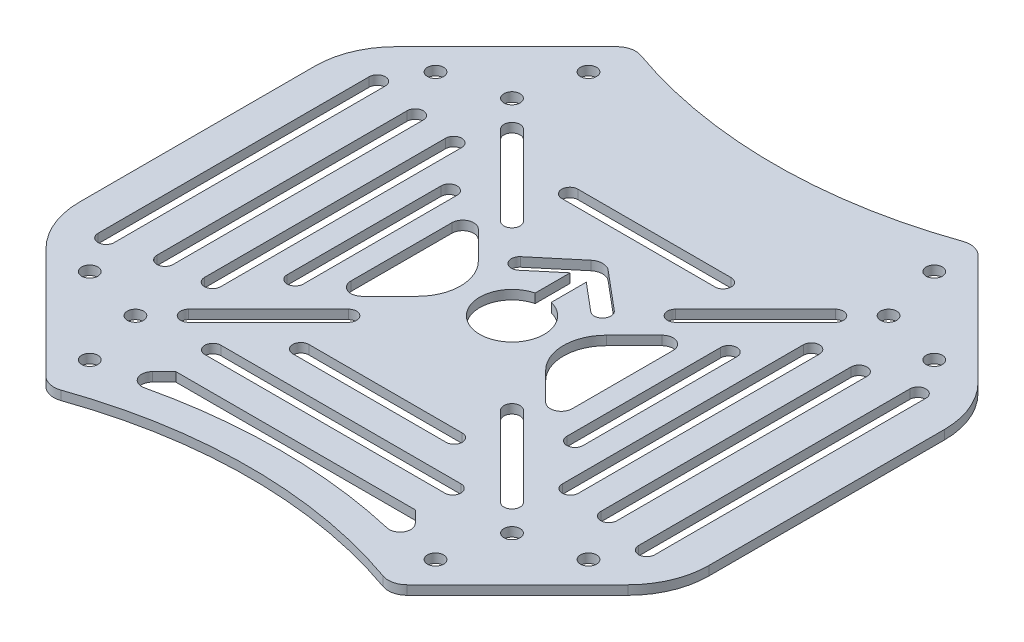
SolidWorks part; units mm, degrees
ref_plane "前基準面" through (0, 0, 0) normal (0, 0, 1) x (1, 0, 0)
ref_plane "上基準面" through (0, 0, 0) normal (0, 1, 0) x (1, 0, 0)
ref_plane "右基準面" through (0, 0, 0) normal (1, 0, 0) x (0, 0, -1)
sketch "草圖1" plane through (0, 0, 0) normal (0, 1, 0) x (1, 0, 0)
  line L0 (-88.3224, -92.0235) -> (-10.6127, -92.0235) construction
  line L1 (-96.5414, 45.9038) -> (-96.5414, -104.0962) construction
  line L2 (0, 5.7817) -> (0, -5.7817) construction
  line L3 (-13.0005, 0) -> (13.0005, 0) construction
  line L4 (-14.25, 25) -> (14.25, 25) construction
  line L5 (-14.25, 26.5) -> (14.25, 26.5)
  line L6 (-14.25, 23.5) -> (14.25, 23.5)
  line L7 (-14.25, -25) -> (14.25, -25) construction
  line L8 (-14.25, -26.5) -> (14.25, -26.5)
  line L9 (-14.25, -23.5) -> (14.25, -23.5)
  line L10 (-47.2341, 47.2341) -> (47.2341, -47.2341) construction
  line L11 (47.2341, 47.2341) -> (-47.2341, -47.2341) construction
  line L12 (-30.052, 30.052) -> (-15.2028, 15.2028) construction
  line L13 (-28.9914, 31.1127) -> (-14.1421, 16.2635)
  line L14 (-31.1127, 28.9914) -> (-16.2635, 14.1421)
  line L15 (30.052, 30.052) -> (15.2028, 15.2028) construction
  line L16 (28.9914, 31.1127) -> (14.1421, 16.2635)
  line L17 (31.1127, 28.9914) -> (16.2635, 14.1421)
  line L18 (30.052, -30.052) -> (15.2028, -15.2028) construction
  line L19 (28.9914, -31.1127) -> (14.1421, -16.2635)
  line L20 (31.1127, -28.9914) -> (16.2635, -14.1421)
  line L21 (-30.052, -30.052) -> (-15.2028, -15.2028) construction
  line L22 (-28.9914, -31.1127) -> (-14.1421, -16.2635)
  line L23 (-31.1127, -28.9914) -> (-16.2635, -14.1421)
  line L24 (-33.25, 22.4) -> (-33.25, -22.4) construction
  line L25 (-31.75, 22.4) -> (-31.75, -22.4)
  line L26 (-34.75, 22.4) -> (-34.75, -22.4)
  line L27 (-41.25, 23.25) -> (-41.25, -23.25) construction
  line L28 (-39.75, 23.25) -> (-39.75, -23.25)
  line L29 (-42.75, 23.25) -> (-42.75, -23.25)
  line L30 (-50.25, 25.2) -> (-50.25, -25.2) construction
  line L31 (-48.75, 25.2) -> (-48.75, -25.2)
  line L32 (-51.75, 25.2) -> (-51.75, -25.2)
  line L33 (50.25, 25.2) -> (50.25, -25.2) construction
  line L34 (48.75, 25.2) -> (48.75, -25.2)
  line L35 (51.75, 25.2) -> (51.75, -25.2)
  line L36 (41.25, 23.25) -> (41.25, -23.25) construction
  line L37 (39.75, 23.25) -> (39.75, -23.25)
  line L38 (42.75, 23.25) -> (42.75, -23.25)
  line L39 (33.25, 22.4) -> (33.25, -22.4) construction
  line L40 (31.75, 22.4) -> (31.75, -22.4)
  line L41 (34.75, 22.4) -> (34.75, -22.4)
  line L42 (-26, 14.3) -> (-26, -14.3) construction
  line L43 (-24.5, 14.3) -> (-24.5, -14.3)
  line L44 (-27.5, 14.3) -> (-27.5, -14.3)
  line L45 (-1.5, 5.8095) -> (-1.5, 12.3095)
  line L46 (-1.5, 12.3095) -> (-6.7013, 7.9451)
  line L47 (-8.6939, 10.3198) -> (-1.607, 16.2665)
  line L48 (8.6939, 10.3198) -> (1.607, 16.2665)
  line L49 (1.5, 5.8095) -> (1.5, 12.3095)
  line L50 (1.5, 12.3095) -> (6.7013, 7.9451)
  line L51 (26, 14.3) -> (26, -14.3) construction
  line L52 (24.5, 14.3) -> (24.5, -14.3)
  line L53 (27.5, 14.3) -> (27.5, -14.3)
  line L54 (-22.3, -33.3) -> (22.3, -33.3) construction
  line L55 (-22.3, -31.8) -> (22.3, -31.8)
  line L56 (-22.3, -34.8) -> (22.3, -34.8)
  line L57 (-31.9883, -54.6323) -> (-58.5, -28.1206)
  line L58 (-58.5, -28.1206) -> (-58.5, 28.1206)
  line L59 (31.9883, -54.6323) -> (58.5, -28.1206)
  line L60 (58.5, -28.1206) -> (58.5, 28.1206)
  line L61 (-31.9883, 54.6323) -> (-58.5, 28.1206)
  line L62 (31.9883, 54.6323) -> (58.5, 28.1206)
  line L63 (20.5663, -9.3678) -> (20.5663, 9.3678)
  line L64 (17.0742, 10.8143) -> (11.9044, 5.6446)
  line L65 (17.0742, -10.8143) -> (11.9044, -5.6446)
  line L66 (-17.0742, -10.8143) -> (-11.9044, -5.6446)
  line L67 (-17.0742, 10.8143) -> (-11.9044, 5.6446)
  line L68 (-20.5663, -9.3678) -> (-20.5663, 9.3678)
  line L69 (-22.2619, -40.2376) -> (22.2619, -40.2376)
  line L70 (22.2619, -40.2376) -> (24.4317, -42.4074)
  line L71 (-22.2619, -40.2376) -> (-24.4317, -42.4074)
  line L72 (32.138, 46.3508) -> (46.3508, 32.138) construction
  line L73 (3.7413, -66.2623) -> (66.2623, -3.7413) construction
  arc A0 (-14.25, 26.5) -> (-14.25, 23.5) centre (-14.25, 25) ccw
  arc A1 (14.25, 23.5) -> (14.25, 26.5) centre (14.25, 25) ccw
  arc A2 (-14.25, -26.5) -> (-14.25, -23.5) centre (-14.25, -25) cw
  arc A3 (14.25, -23.5) -> (14.25, -26.5) centre (14.25, -25) cw
  circle A4 centre (-35.0018, 35.0018) radius 1.5
  circle A5 centre (35.0018, -35.0018) radius 1.5
  circle A6 centre (-35.0018, -35.0018) radius 1.5
  circle A7 centre (35.0018, 35.0018) radius 1.5
  arc A8 (-28.9914, 31.1127) -> (-31.1127, 28.9914) centre (-30.052, 30.052) ccw
  arc A9 (-16.2635, 14.1421) -> (-14.1421, 16.2635) centre (-15.2028, 15.2028) ccw
  arc A10 (28.9914, 31.1127) -> (31.1127, 28.9914) centre (30.052, 30.052) cw
  arc A11 (16.2635, 14.1421) -> (14.1421, 16.2635) centre (15.2028, 15.2028) cw
  arc A12 (28.9914, -31.1127) -> (31.1127, -28.9914) centre (30.052, -30.052) ccw
  arc A13 (16.2635, -14.1421) -> (14.1421, -16.2635) centre (15.2028, -15.2028) ccw
  arc A14 (-28.9914, -31.1127) -> (-31.1127, -28.9914) centre (-30.052, -30.052) cw
  arc A15 (-16.2635, -14.1421) -> (-14.1421, -16.2635) centre (-15.2028, -15.2028) cw
  arc A16 (-31.75, 22.4) -> (-34.75, 22.4) centre (-33.25, 22.4) ccw
  arc A17 (-34.75, -22.4) -> (-31.75, -22.4) centre (-33.25, -22.4) ccw
  arc A18 (-39.75, 23.25) -> (-42.75, 23.25) centre (-41.25, 23.25) ccw
  arc A19 (-42.75, -23.25) -> (-39.75, -23.25) centre (-41.25, -23.25) ccw
  arc A20 (-48.75, 25.2) -> (-51.75, 25.2) centre (-50.25, 25.2) ccw
  arc A21 (-51.75, -25.2) -> (-48.75, -25.2) centre (-50.25, -25.2) ccw
  arc A22 (48.75, 25.2) -> (51.75, 25.2) centre (50.25, 25.2) cw
  arc A23 (51.75, -25.2) -> (48.75, -25.2) centre (50.25, -25.2) cw
  arc A24 (39.75, 23.25) -> (42.75, 23.25) centre (41.25, 23.25) cw
  arc A25 (42.75, -23.25) -> (39.75, -23.25) centre (41.25, -23.25) cw
  arc A26 (31.75, 22.4) -> (34.75, 22.4) centre (33.25, 22.4) cw
  arc A27 (34.75, -22.4) -> (31.75, -22.4) centre (33.25, -22.4) cw
  arc A28 (-24.5, 14.3) -> (-27.5, 14.3) centre (-26, 14.3) ccw
  arc A29 (-27.5, -14.3) -> (-24.5, -14.3) centre (-26, -14.3) ccw
  arc A30 (-1.5, 5.8095) -> (1.5, 5.8095) centre (0, 0) ccw
  arc A31 (-6.7013, 7.9451) -> (-8.6939, 10.3198) centre (-7.6976, 9.1325) cw
  arc A32 (-1.607, 16.2665) -> (1.607, 16.2665) centre (0, 14.3514) cw
  arc A33 (6.7013, 7.9451) -> (8.6939, 10.3198) centre (7.6976, 9.1325) ccw
  circle A34 centre (-32.138, -46.3508) radius 1.5
  circle A35 centre (-46.3508, -32.138) radius 1.5
  circle A36 centre (-32.138, 46.3508) radius 1.5
  circle A37 centre (-46.3508, 32.138) radius 1.5
  circle A38 centre (46.3508, 32.138) radius 1.5
  circle A39 centre (32.138, 46.3508) radius 1.5
  circle A40 centre (32.138, -46.3508) radius 1.5
  circle A41 centre (46.3508, -32.138) radius 1.5
  arc A42 (24.5, 14.3) -> (27.5, 14.3) centre (26, 14.3) cw
  arc A43 (27.5, -14.3) -> (24.5, -14.3) centre (26, -14.3) cw
  arc A44 (-22.3, -31.8) -> (-22.3, -34.8) centre (-22.3, -33.3) ccw
  arc A45 (22.3, -34.8) -> (22.3, -31.8) centre (22.3, -33.3) ccw
  arc A46 (-31.9883, -54.6323) -> (31.9883, -54.6323) centre (0, -138.7558) cw
  arc A47 (-31.9883, 54.6323) -> (31.9883, 54.6323) centre (0, 138.7558) ccw
  arc A48 (11.9044, -5.6446) -> (11.9044, 5.6446) centre (17.549, 0) cw
  arc A49 (20.5663, 9.3678) -> (17.0742, 10.8143) centre (18.5207, 9.3678) ccw
  arc A50 (20.5663, -9.3678) -> (17.0742, -10.8143) centre (18.5207, -9.3678) cw
  arc A51 (-20.5663, -9.3678) -> (-17.0742, -10.8143) centre (-18.5207, -9.3678) ccw
  arc A52 (-11.9044, -5.6446) -> (-11.9044, 5.6446) centre (-17.549, 0) ccw
  arc A53 (-20.5663, 9.3678) -> (-17.0742, 10.8143) centre (-18.5207, 9.3678) cw
  arc A54 (24.4317, -42.4074) -> (22.5661, -45.77) centre (23.0175, -43.8216) cw
  arc A55 (22.5661, -45.77) -> (0, -43.1906) centre (0, -143.1906) ccw
  arc A56 (-24.4317, -42.4074) -> (-22.5661, -45.77) centre (-23.0175, -43.8216) ccw
  arc A57 (-22.5661, -45.77) -> (0, -43.1906) centre (0, -143.1906) cw
  point P8 (0, 0)
  point P11 (0, 0)
  point P12 (0, 25)
  point P23 (0, -25)
  point P32 (0, 0)
  point P40 (-22.6274, 22.6274)
  point P48 (22.6274, 22.6274)
  point P55 (22.6274, -22.6274)
  point P62 (-22.6274, -22.6274)
  point P68 (-33.25, 0)
  point P74 (-41.25, 0)
  point P82 (-50.25, 0)
  point P88 (-26, 0)
  point P95 (50.25, 0)
  point P102 (41.25, 0)
  point P109 (33.25, 0)
  point P129 (0, -33.3)
  point P148 (0, 0)
  point P155 (26, 0)
  point P178 (-58.5, 0)
  point P179 (58.5, 0)
  point P182 (20.5663, 0)
  point P196 (0, 0)
  point P203 (0, -40.2376)
  point P205 (35.0018, -35.0018)
  point P206 (0, 0)
  point P207 (0, 0)
  point P208 (0, 0)
  point P209 (-35.0018, 35.0018)
  point P210 (0, 0)
  point P211 (0, 0)
  point P212 (-6.3312, 8.2556)
  dimension "D5" = 3
  dimension "D10" = 12
  dimension "D11" = 50
  dimension "D15" = 2.5
  dimension "D16" = 3
  dimension "D24" = 90
  dimension "D31" = 100
  dimension "D33" = 2
  dimension "D34" = 3
  dimension "D1" = 150
  dimension "D2" = 3
  dimension "D3" = 50
  dimension "D4" = 6
  dimension "D6" = 3
  dimension "D7" = 3
  dimension "D8" = 3
  dimension "D9" = 3
  dimension "D12" = 6.5
  dimension "D13" = 3
  dimension "D14" = 3.1
  dimension "D18" = 20.1
  dimension "D19" = 52
  dimension "D20" = 66.5
  dimension "D21" = 82.5
  dimension "D22" = 100.5
  dimension "D23" = 3
  dimension "D25" = 117
  dimension "D26" = 122.5
  dimension "D27" = 277.5115
  dimension "D28" = 21
  dimension "D29" = 32
  dimension "D30" = 33.3
  dimension "D32" = 45
  dimension "D35" = 99
  dimension "D36" = 46.5
  dimension "D37" = 28.6
  dimension "D38" = 44.8
  dimension "D39" = 50.4
  dimension "D40" = 28.5
  dimension "D41" = 44.6
  dimension "D42" = 9.3
  dimension "D17" = 4
extrude "填料-伸長1" add sketch "草圖1" along normal blind 1.7
fillet "圓角1" radius 3.5 4 edges at (-31.9883, 0.85, -54.6323) (31.9883, 0.85, -54.6323) (-31.9883, 0.85, 54.6323) (31.9883, 0.85, 54.6323)
fillet "圓角2" radius 15 4 edges at (-58.5, 0.85, 28.1206) (-58.5, 0.85, -28.1206) (58.5, 0.85, -28.1206) (58.5, 0.85, 28.1206)
